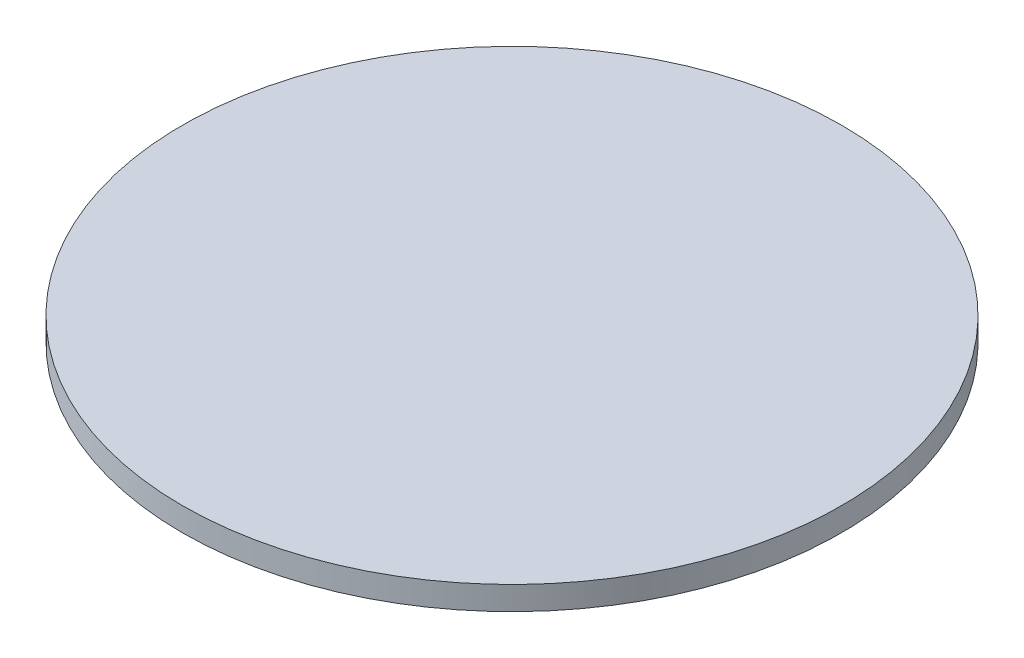
SolidWorks part; units mm, degrees
ref_plane "Front Plane" through (0, 0, 0) normal (0, 0, 1) x (1, 0, 0)
ref_plane "Top Plane" through (0, 0, 0) normal (0, 1, 0) x (1, 0, 0)
ref_plane "Right Plane" through (0, 0, 0) normal (1, 0, 0) x (0, 0, -1)
sketch "Sketch1" plane through (0, 0, 0) normal (0, 1, 0) x (1, 0, 0)
  circle A0 centre (0, 0) radius 1400
  dimension "D1" = 2800
extrude "Boss-Extrude1" add sketch "Sketch1" along normal blind 100
